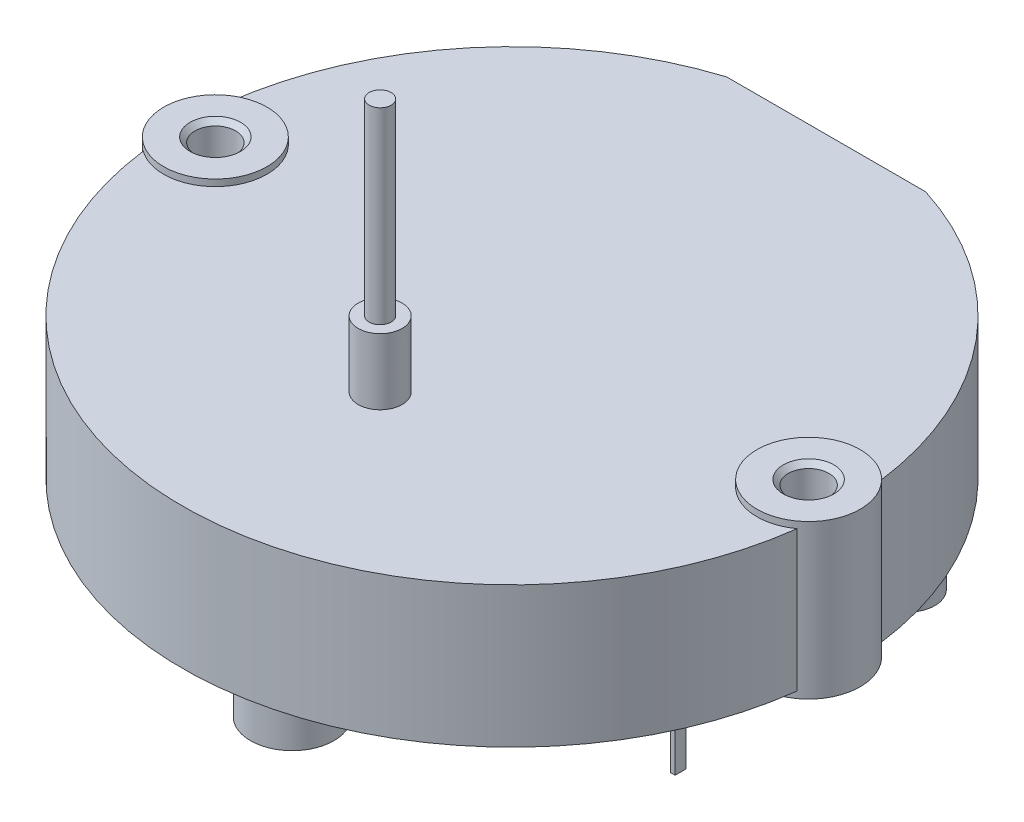
SolidWorks part; units mm, degrees
ref_plane "Front Plane" through (0, 0, 0) normal (0, 0, 1) x (1, 0, 0)
ref_plane "Top Plane" through (0, 0, 0) normal (0, 1, 0) x (1, 0, 0)
ref_plane "Right Plane" through (0, 0, 0) normal (1, 0, 0) x (0, 0, -1)
sketch "Sketch1" plane through (0, 0, 0) normal (0, 1, 0) x (1, 0, 0)
  line L0 (-4.5288, 14.3) -> (4.5288, 14.3)
  arc A0 (-4.5288, 14.3) -> (4.5288, 14.3) centre (0, 0) ccw
  point P5 (0, -15)
  dimension "D1" = 15
  dimension "D2" = 29.3
extrude "Boss-Extrude1" add sketch "Sketch1" along normal blind 6.4
ref_plane "Plane1" through (0, 0, 6) normal (0, 0, 1) x (1, 0, 0)
sketch "Sketch3" plane through (0, 0, 6) normal (0, 0, 1) x (1, 0, 0)
  line L0 (0, 6.4) -> (0, 17.95) construction
  line L1 (15, 6.4) -> (-15, 6.4) construction
  line L2 (0, 17.95) -> (0.5, 17.95)
  line L3 (0.5, 17.95) -> (0.5, 9.4)
  line L4 (0.5, 9.4) -> (1, 9.4)
  line L5 (1, 9.4) -> (1, 6.4)
  line L6 (1, 6.4) -> (0, 6.4)
  line L7 (0, 6.4) -> (0, 17.95)
  dimension "D1" = 17.95
  dimension "D2" = 1
  dimension "D3" = 2
  dimension "D4" = 3
revolve "Revolve1" add sketch "Sketch3" angle 360 about L0
sketch "Sketch4" plane through (0, 6.4, 0) normal (0, 1, 0) x (1, 0, 0)
  line L0 (0, 0) -> (0, 14.3) construction
  line L1 (4.5288, 14.3) -> (-4.5288, 14.3) construction
  circle A0 centre (-13.5, 0) radius 2.35
  dimension "D1" = 4.7
  dimension "D3" = 27
extrude "Boss-Extrude2" add sketch "Sketch4" along normal blind 0.3 and the other way offset from surface (6.7 mm away) 0.3 other way up to face at (0, 0, 0.35)
hole_wizard "Ø1.85 (1.85) Diameter Hole1" positions "Sketch5" profile "Sketch6" hole size "Ø1.85" standard "ANSI Metric" end condition up to next
sketch "Sketch5" plane through (0, -0.3, 0) normal (0, -1, 0) x (-1, 0, 0)
  point P0 (13.5, 0)
sketch "Sketch6" plane through (-13.5, -0.3, 0) normal (1, 0, 0) x (0, 0, -1)
  line L0 (0, 0) -> (0, 7)
  line L1 (0, 7) -> (1.15, 7)
  line L2 (0.925, 6.775) -> (0.925, 0.225)
  line L3 (0.925, 0.225) -> (1.15, 0)
  line L5 (1.15, 0) -> (0, 0)
  line L6 (-0.925, 0.225) -> (-1.15, 0) construction
  line L7 (1.15, 7) -> (0.925, 6.775)
  line L8 (-1.15, 7) -> (-0.925, 6.775) construction
  line L11 (0, -6.35) -> (0, 107.95) construction
  dimension "Thru Hole Dia." = 1.85
  dimension "Thru Hole Depth" = 7
  dimension "Near C'Sink Dia." = 2.3
  dimension "Near C'Sink Angle" = 90
  dimension "Far C'Sink Dia." = 2.3
  dimension "Far C'Sink Angle" = 90
mirror "Mirror1" about plane through (0, 0, 0) normal (1, 0, 0) of "Boss-Extrude2", "Ø1.85 (1.85) Diameter Hole1"
sketch "Sketch7" plane through (0, 0, 0) normal (0, -1, 0) x (1, 0, 0)
  circle A0 centre (0, 10) radius 1.9
  circle A1 centre (9, -9) radius 1.25
  dimension "D2" = 3.8
  dimension "D5" = 2.5
  dimension "D1" = 10
  dimension "D3" = 9
  dimension "D4" = 19
extrude "Boss-Extrude3" add sketch "Sketch7" along normal blind 4.4
sketch "Sketch8" plane through (0, 0, 0) normal (0, -1, 0) x (-1, 0, 0)
  line L0 (-11.325, -4.1) -> (-11.525, -4.1)
  line L1 (11.525, -4.1) -> (11.325, -4.1)
  line L2 (11.525, -4.1) -> (11.525, -3.6)
  line L3 (11.525, -3.6) -> (11.325, -3.6)
  line L4 (11.325, -4.1) -> (11.325, -3.6)
  line L5 (11.525, -4.1) -> (11.325, -3.6) construction
  line L6 (11.525, -3.6) -> (11.325, -4.1) construction
  line L7 (-11.325, -4.1) -> (-11.325, -3.6)
  line L8 (-11.325, -3.6) -> (-11.525, -3.6)
  line L9 (-11.525, -4.1) -> (-11.525, -3.6)
  line L10 (-11.325, -4.1) -> (-11.525, -3.6) construction
  line L11 (-11.325, -3.6) -> (-11.525, -4.1) construction
  line L12 (-11.325, 3.6) -> (-11.525, 3.6)
  line L13 (-11.325, 3.6) -> (-11.325, 4.1)
  line L14 (-11.325, 4.1) -> (-11.525, 4.1)
  line L15 (-11.525, 3.6) -> (-11.525, 4.1)
  line L16 (-11.325, 3.6) -> (-11.525, 4.1) construction
  line L17 (-11.325, 4.1) -> (-11.525, 3.6) construction
  line L18 (11.525, 3.6) -> (11.325, 3.6)
  line L19 (11.525, 3.6) -> (11.525, 4.1)
  line L20 (11.525, 4.1) -> (11.325, 4.1)
  line L21 (11.325, 3.6) -> (11.325, 4.1)
  line L22 (11.525, 3.6) -> (11.325, 4.1) construction
  line L23 (11.525, 4.1) -> (11.325, 3.6) construction
  line L24 (11.425, -3.85) -> (-11.425, -3.85) construction
  line L25 (11.425, -3.85) -> (11.425, 3.85) construction
  point P0 (11.425, -3.85)
  point P6 (-11.425, -3.85)
  point P12 (-11.425, 3.85)
  point P17 (11.425, 3.85)
  dimension "D1" = 0.5
  dimension "D2" = 0.2
  dimension "D5" = 22.85
  dimension "D6" = 7.7
  dimension "D7" = 11.425
  dimension "D8" = 3.85
  dimension "D3" = 2
  dimension "D4" = 2
extrude "Boss-Extrude4" add sketch "Sketch8" along normal blind 3.9
